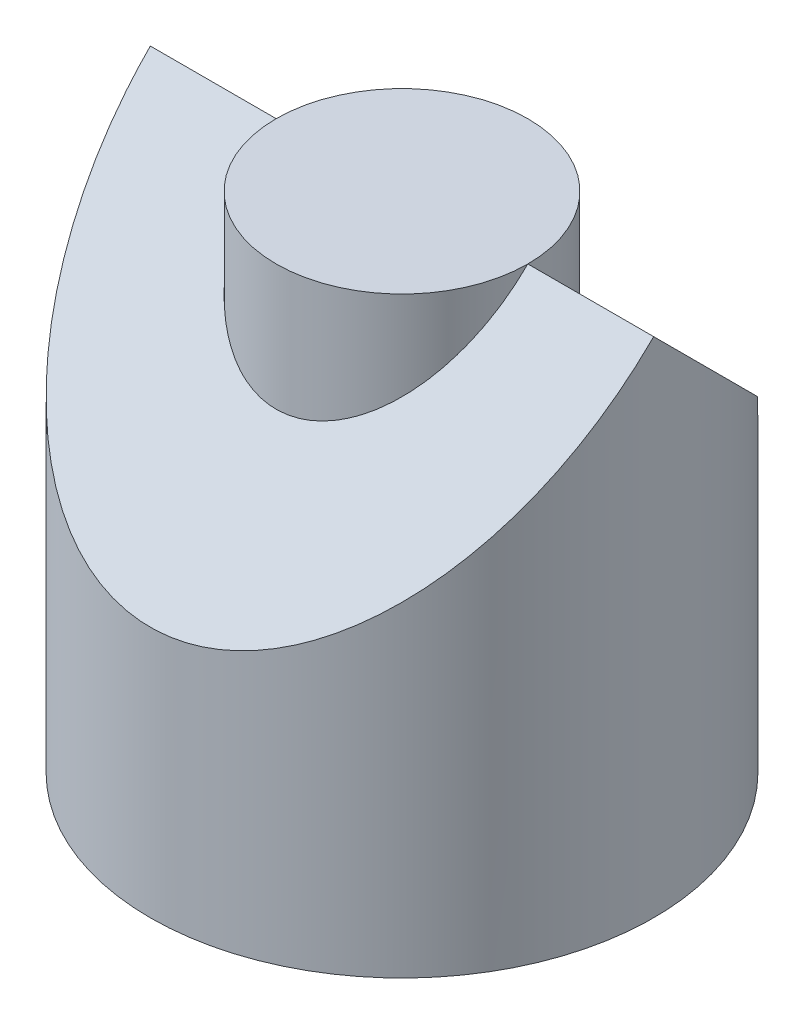
SolidWorks part; units mm, degrees
ref_plane "Front" through (0, 0, 0) normal (0, 0, 1) x (1, 0, 0)
ref_plane "Top" through (0, 0, 0) normal (0, 1, 0) x (1, 0, 0)
ref_plane "Right" through (0, 0, 0) normal (1, 0, 0) x (0, 0, -1)
sketch "Sketch1" plane through (0, 0, 0) normal (0, 1, 0) x (1, 0, 0)
  circle A0 centre (0, 0) radius 2
  circle A1 centre (0, 0) radius 1
  dimension "D1" = 4
  dimension "D2" = 2
extrude "Boss-Extrude1" add sketch "Sketch1" along normal blind 4
sketch "Sketch2" plane through (0, 0, 0) normal (1, 0, 0) x (0, 0, -1)
  line L0 (-2, 2) -> (0, 4)
  line L1 (-2, 4) -> (-2, 0) construction
  line L2 (2, 4) -> (-2, 4) construction
  line L3 (0, 4) -> (2, 2)
  line L4 (2, 0) -> (2, 4) construction
  line L5 (2, 2) -> (2, 4)
  line L6 (2, 4) -> (-2, 4)
  line L7 (-2, 4) -> (-2, 2)
extrude "Cut-Extrude1" cut sketch "Sketch2" against normal mid plane 4 contours L5 L6 L3 | L6 L7 L0
sketch "Sketch3" plane through (0, 0, 0) normal (0, -1, 0) x (1, 0, 0)
  circle A0 centre (0, 0) radius 1
extrude "Boss-Extrude2" add sketch "Sketch3" against normal blind 4 separate body
